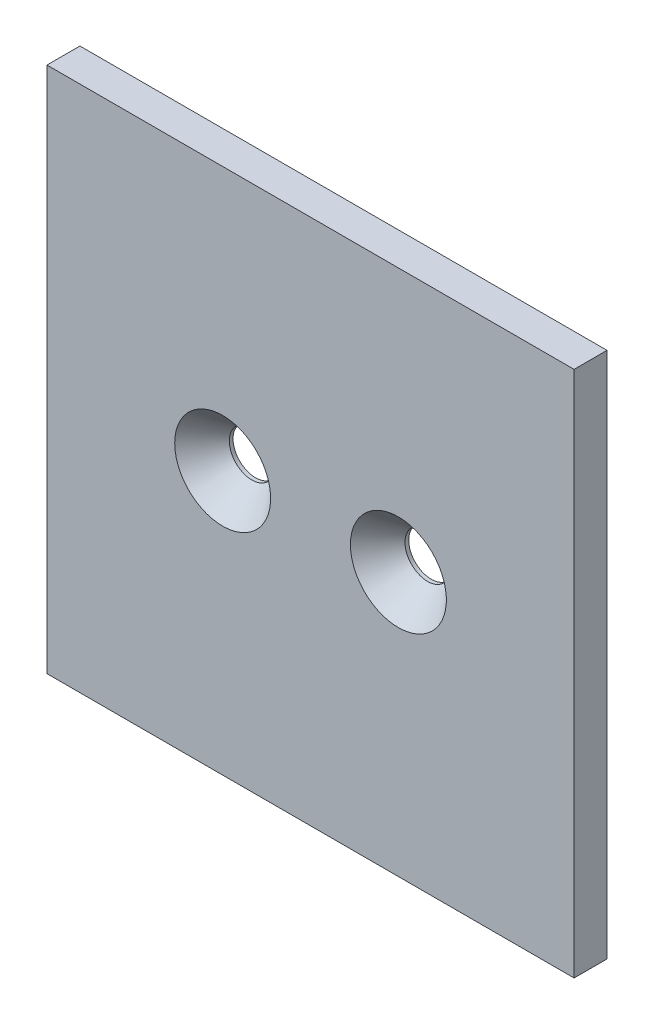
SolidWorks part; units mm, degrees
ref_plane "Front" through (0, 0, 0) normal (0, 0, 1) x (1, 0, 0)
ref_plane "Top" through (0, 0, 0) normal (0, 1, 0) x (1, 0, 0)
ref_plane "Right" through (0, 0, 0) normal (1, 0, 0) x (0, 0, -1)
sketch "Sketch1" plane through (0, 0, 0) normal (0, 0, 1) x (1, 0, 0)
  line L0 (-12.7, 0) -> (12.7, 0) construction
  line L1 (-38.1, 38.1) -> (38.1, 38.1)
  line L2 (-38.1, 38.1) -> (-38.1, -38.1)
  line L3 (-38.1, -38.1) -> (38.1, -38.1)
  line L4 (38.1, 38.1) -> (38.1, -38.1)
  line L5 (-38.1, 38.1) -> (38.1, -38.1) construction
  line L6 (-38.1, -38.1) -> (38.1, 38.1) construction
  circle A0 centre (-12.7, 0) radius 3.2639
  circle A1 centre (12.7, 0) radius 3.2639
  point P0 (0, 0)
  dimension "HoleDiameter" = 6.5278
  dimension "Width" = 76.2
  dimension "Height" = 76.2
  dimension "HoleSpacing" = 25.4
extrude "Boss-Extrude1" add sketch "Sketch1" along normal mid plane 4.7625
sketch "Sketch2" plane through (0, 0, 0) normal (0, 1, 0) x (1, 0, 0)
  line L0 (-12.7, 2.3813) -> (-12.7, -2.3813) construction
  line L1 (-9.4361, 2.3813) -> (-15.9639, 2.3813) construction
  line L2 (-15.9639, -2.3813) -> (-9.4361, -2.3813) construction
  line L3 (-5.7658, -2.3812) -> (-12.7, 5.5956)
  line L4 (-38.1, -2.3813) -> (38.1, -2.3813) construction
  line L5 (-12.7, 5.5956) -> (-12.7, -2.3813)
  line L6 (-12.7, -2.3813) -> (-5.7658, -2.3812)
  line L7 (-12.7, 5.5956) -> (-19.6342, -2.3812) construction
  dimension "CSinkDiameter" = 13.8684
  dimension "D2" = 82
revolve "Cut-Revolve1" cut sketch "Sketch2" angle 360 about L5
sketch "Sketch3" plane through (0, 0, 2.3813) normal (0, 0, 1) x (1, 0, 0)
  point P0 (12.7, 0)
pattern_sketch "Sketch-Pattern1" of "Cut-Revolve1" driven by "Sketch3"
sketch "Sketch4" plane through (0, 0, 0) normal (1, 0, 0) x (0, 0, -1)
  line L0 (1.8409, 3.2639) -> (1.8409, -3.2639) construction
  line L1 (-2.3813, 6.9342) -> (-2.3813, -6.9342) construction
  line L2 (1.8409, 3.2639) -> (1.8409, -3.2639)
  line L3 (-2.3813, 6.9342) -> (-2.3813, -6.9342) construction
  line L4 (-2.3813, 6.9342) -> (1.8409, 3.2639)
  line L5 (1.8409, 3.2639) -> (2.3813, 3.2639)
  line L6 (2.3813, -38.1) -> (2.3813, 38.1) construction
  line L7 (-2.3813, -6.9342) -> (1.8409, -3.2639)
  line L8 (1.8409, -3.2639) -> (2.3813, -3.2639)
ref_plane "CenterPlane1" through (0, 0, 0) normal (-1, 0, 0) x (0, 0, 1)
